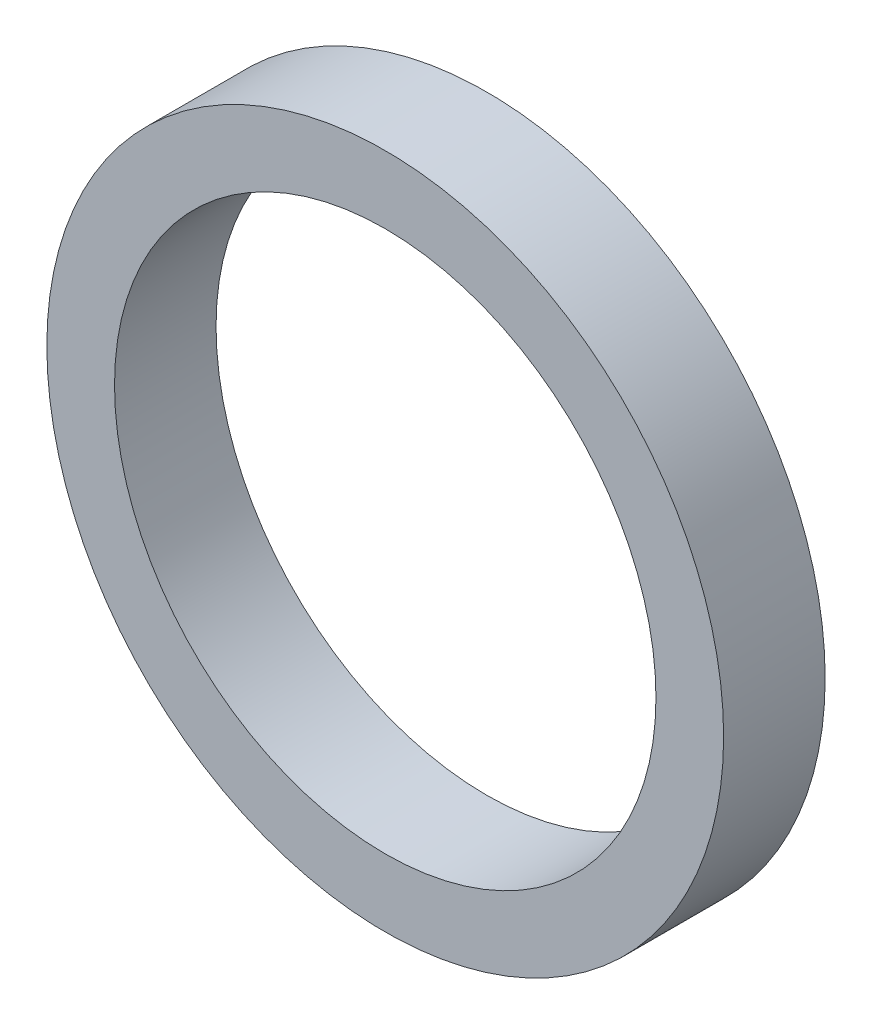
SolidWorks part; units mm, degrees
ref_plane "Front Plane" through (0, 0, 0) normal (0, 0, 1) x (1, 0, 0)
ref_plane "Top Plane" through (0, 0, 0) normal (0, 1, 0) x (1, 0, 0)
ref_plane "Right Plane" through (0, 0, 0) normal (1, 0, 0) x (0, 0, -1)
sketch "Sketch1" plane through (0, 0, 0) normal (0, 0, 1) x (1, 0, 0)
  circle A0 centre (0, 0) radius 8
  circle A1 centre (0, 0) radius 10
  dimension "D1" = 16
  dimension "D2" = 20
extrude "Boss-Extrude1" add sketch "Sketch1" along normal blind 3
